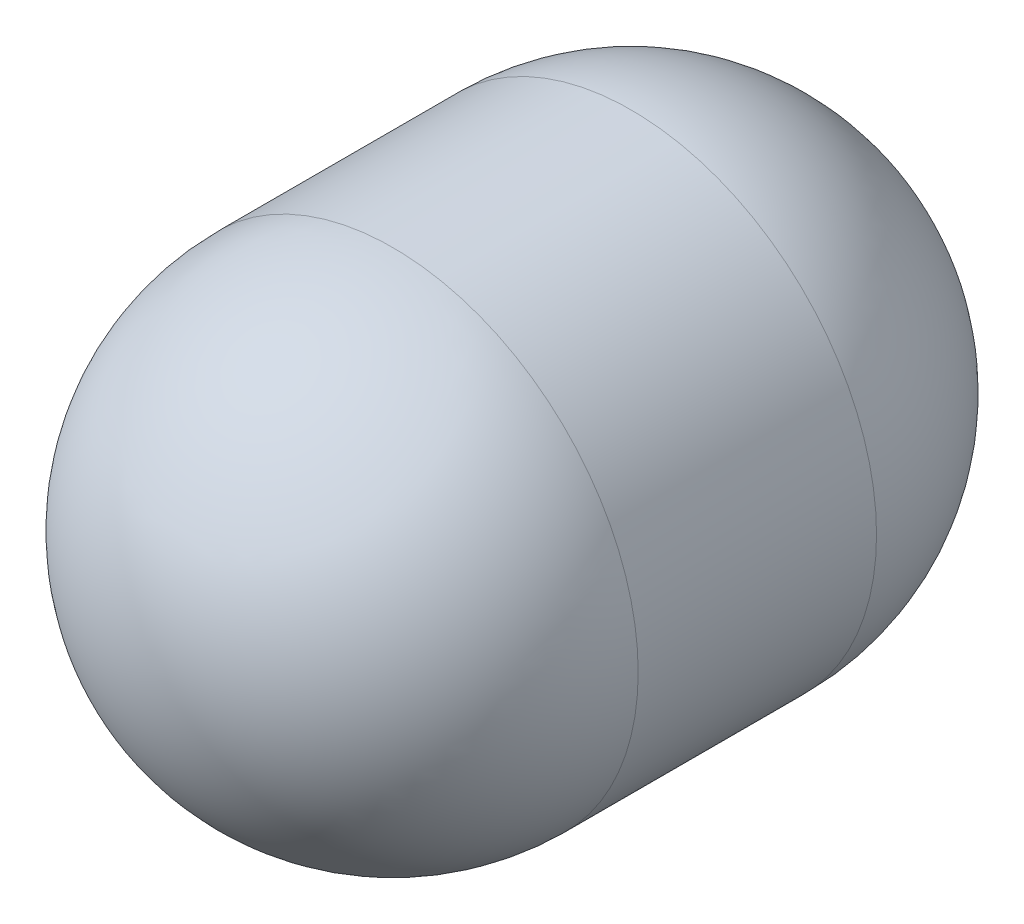
SolidWorks part; units mm, degrees
material "Wet Tank mat'l"
ref_plane "Front Plane" through (0, 0, 0) normal (0, 0, 1) x (1, 0, 0)
ref_plane "Top Plane" through (0, 0, 0) normal (0, 1, 0) x (1, 0, 0)
ref_plane "Right Plane" through (0, 0, 0) normal (1, 0, 0) x (0, 0, -1)
sketch "Sketch1" plane through (0, 0, 0) normal (0, 1, 0) x (1, 0, 0)
  line L0 (0, 0) -> (55.5625, 0) construction
  line L1 (55.5625, -26.9875) -> (55.5625, 26.9875)
  line L2 (0, 80.6816) -> (14.2875, 80.6816) construction
  line L3 (0, 26.9875) -> (0, 0) construction
  line L4 (0, 26.9875) -> (0, 80.6816) construction
  line L5 (0, 80.6816) -> (14.2875, 80.6816)
  line L6 (0, 80.6816) -> (0, -82.55)
  arc A1 (55.5625, 26.9875) -> (14.2875, 80.6816) centre (0, 26.9875) ccw
  arc A2 (55.5625, -26.9875) -> (0, -82.55) centre (0, -26.9875) cw
  point P2 (9.6969, -104.9068)
  point P7 (55.5625, 0)
  point P11 (0, -82.55)
  dimension "D3" = 55.5625
  dimension "D1" = 55.5625
  dimension "D2" = 53.975
  dimension "D5" = 14.2875
revolve "Revolve1" add sketch "Sketch1" angle 360 about L6
sketch "Sketch2" plane through (0, 0, -80.6816) normal (0, 0, -1) x (-1, 0, 0)
  circle A0 centre (0, 0) radius 14.2875
